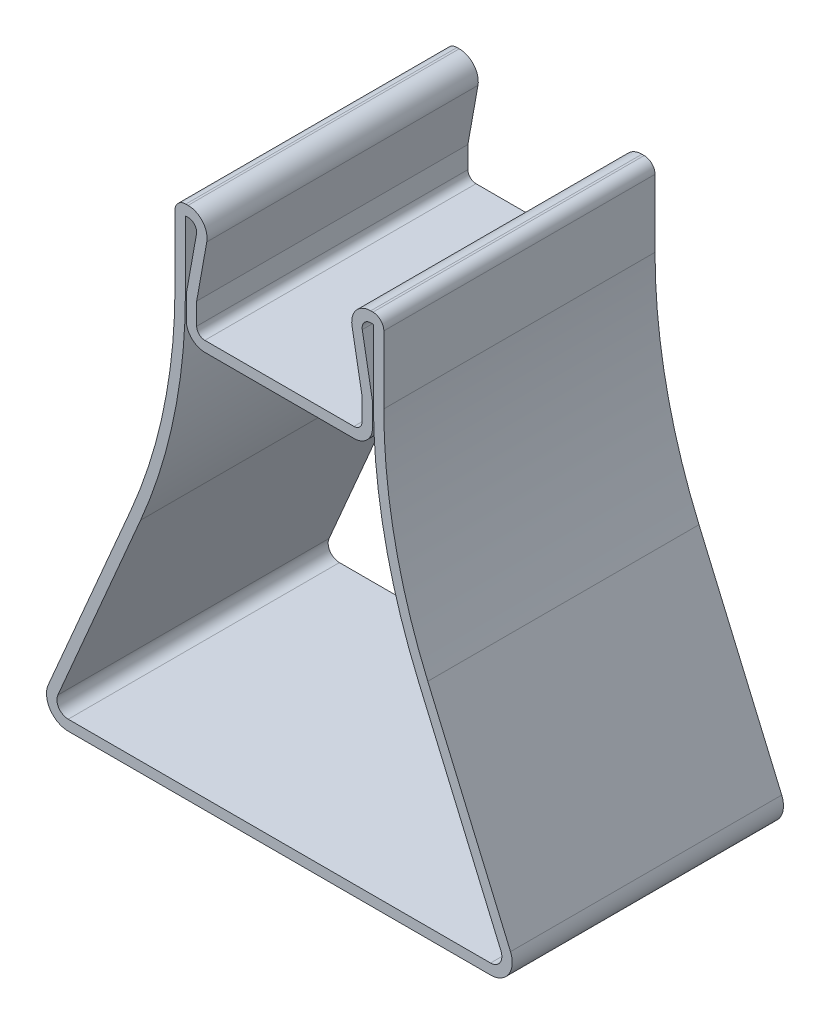
SolidWorks part; units mm, degrees
material "ABS eSun"
ref_plane "Front Plane" through (0, 0, 0) normal (0, 0, 1) x (1, 0, 0)
ref_plane "Top Plane" through (0, 0, 0) normal (0, 1, 0) x (1, 0, 0)
ref_plane "Right Plane" through (0, 0, 0) normal (1, 0, 0) x (0, 0, -1)
sketch "Sketch1" plane through (0, 0, 0) normal (0, 0, 1) x (1, 0, 0)
  line L0 (-15.25, 0) -> (15.25, 0)
  line L1 (15.25, 0) -> (15.25, 5.5)
  line L2 (15.25, 20) -> (19.25, 20)
  line L3 (19.25, 20) -> (19.25, -15)
  line L4 (19.25, -15) -> (45, -75)
  line L5 (45, -75) -> (-45, -75)
  line L6 (-45, -75) -> (-19.25, -15)
  line L7 (-19.25, -15) -> (-19.25, 20)
  line L8 (-19.25, 20) -> (-15.25, 20)
  line L9 (-15.25, 5.5) -> (-15.25, 0)
  line L10 (-15.25, 20) -> (-12.65, 20)
  line L19 (-12.65, 20) -> (-15.25, 5.5)
  line L20 (-15.25, 20) -> (-15.25, 5.5) construction
  line L21 (15.25, 20) -> (12.65, 20)
  line L22 (12.65, 20) -> (15.25, 5.5)
  line L23 (-15.25, 5.5) -> (15.25, 5.5) construction
  line L24 (15.25, 5.5) -> (15.25, 20) construction
  point P3 (0, -75)
  dimension "D1" = 30.5
  dimension "D2" = 75
  dimension "D3" = 90
  dimension "D4" = 4
  dimension "D5" = 20
  dimension "D6" = 60
  dimension "D7" = 2.6
  dimension "D8" = 14.5
extrude "main_boss" add sketch "Sketch1" along normal mid plane 50
fillet "fillet shoulder" radius 100 2 edges at (-19.25, -15, 0) (19.25, -15, 0)
fillet "fillet base" radius 4 2 edges at (-45, -75, 0) (45, -75, 0)
fillet "fillet top" radius 2 2 edges at (-19.25, 20, 0) (19.25, 20, 0)
fillet "fillet groove" radius 1.5 2 edges at (15.25, 0, 0) (-15.25, 0, 0)
fillet "fillet_tops" radius 3.5 2 edges at (-12.65, 20, 0) (12.65, 20, 0)
sketch "Sketch3" plane through (0, 0, 25) normal (0, 0, 1) x (1, 0, 0)
  line L20 (15.2782, 16.2211) -> (17.17, 5.6708)
  line L21 (17.17, 5.6708) -> (17.17, 1.5)
  line L22 (13.75, -1.92) -> (-13.75, -1.92)
  line L23 (-17.17, 1.5) -> (-17.17, 5.6708)
  line L24 (-17.17, 5.6708) -> (-15.2782, 16.2211)
  line L25 (-17.33, 18) -> (-17.33, 5.552)
  line L26 (-25.5909, -34.6434) -> (-40.8419, -70.1797)
  line L27 (-38.9305, -73.08) -> (38.9305, -73.08)
  line L28 (40.8419, -70.1797) -> (25.5909, -34.6434)
  line L29 (17.33, 5.552) -> (17.33, 18)
  line L30 (15.2782, 16.2211) -> (17.17, 5.6708)
  line L31 (17.17, 5.6708) -> (17.17, 1.5)
  line L32 (13.75, -1.92) -> (-13.75, -1.92)
  line L33 (-17.17, 1.5) -> (-17.17, 5.6708)
  line L34 (-17.17, 5.6708) -> (-15.2782, 16.2211)
  line L35 (-17.33, 18) -> (-17.33, 5.552)
  line L36 (-25.5909, -34.6434) -> (-40.8419, -70.1797)
  line L37 (-38.9305, -73.08) -> (38.9305, -73.08)
  line L38 (40.8419, -70.1797) -> (25.5909, -34.6434)
  line L39 (17.33, 5.552) -> (17.33, 18)
  line L42 (17.25, 18.08) -> (16.8334, 18.08)
  line L43 (17.25, 18.08) -> (16.8334, 18.08)
  line L44 (-16.8334, 18.08) -> (-17.25, 18.08)
  line L45 (-16.8334, 18.08) -> (-17.25, 18.08)
  arc A20 (17.33, 18) -> (17.25, 18.08) centre (17.25, 18) ccw
  arc A21 (16.8334, 18.08) -> (15.2782, 16.2211) centre (16.8334, 16.5) ccw
  arc A22 (13.75, -1.92) -> (17.17, 1.5) centre (13.75, 1.5) ccw
  arc A23 (-17.17, 1.5) -> (-13.75, -1.92) centre (-13.75, 1.5) ccw
  arc A24 (-15.2782, 16.2211) -> (-16.8334, 18.08) centre (-16.8334, 16.5) ccw
  arc A25 (-17.25, 18.08) -> (-17.33, 18) centre (-17.25, 18) ccw
  arc A26 (-25.5909, -34.6434) -> (-17.33, 5.552) centre (-119.25, 5.552) ccw
  arc A27 (-40.8419, -70.1797) -> (-38.9305, -73.08) centre (-38.9305, -71) ccw
  arc A28 (38.9305, -73.08) -> (40.8419, -70.1797) centre (38.9305, -71) ccw
  arc A29 (17.33, 5.552) -> (25.5909, -34.6434) centre (119.25, 5.552) ccw
  arc A30 (17.33, 18) -> (17.25, 18.08) centre (17.25, 18) ccw
  arc A31 (16.8334, 18.08) -> (15.2782, 16.2211) centre (16.8334, 16.5) ccw
  arc A32 (13.75, -1.92) -> (17.17, 1.5) centre (13.75, 1.5) ccw
  arc A33 (-17.17, 1.5) -> (-13.75, -1.92) centre (-13.75, 1.5) ccw
  arc A34 (-15.2782, 16.2211) -> (-16.8334, 18.08) centre (-16.8334, 16.5) ccw
  arc A35 (-17.25, 18.08) -> (-17.33, 18) centre (-17.25, 18) ccw
  arc A36 (-25.5909, -34.6434) -> (-17.33, 5.552) centre (-119.25, 5.552) ccw
  arc A37 (-40.8419, -70.1797) -> (-38.9305, -73.08) centre (-38.9305, -71) ccw
  arc A38 (38.9305, -73.08) -> (40.8419, -70.1797) centre (38.9305, -71) ccw
  arc A39 (17.33, 5.552) -> (25.5909, -34.6434) centre (119.25, 5.552) ccw
  dimension "D1" = 1.92
extrude "cut_to_thickness" cut sketch "Sketch3" against normal through all
sketch "Sketch4" plane through (0, -73.08, 0) normal (0, 1, 0) x (1, 0, 0)
  line L0 (32.7275, 19) -> (-3.312, 19) construction
  line L1 (-38.9305, 25) -> (38.9305, 25) construction
  text T0 "V1.4" font "DS ISO 1" height 6.5
  dimension "D1" = 6
extrude "version_no" cut sketch "Sketch4" against normal blind 0.25
equation "\"wall_thickness\"=1.92"
equation "\"D1@Sketch3\"=\"wall_thickness\""
